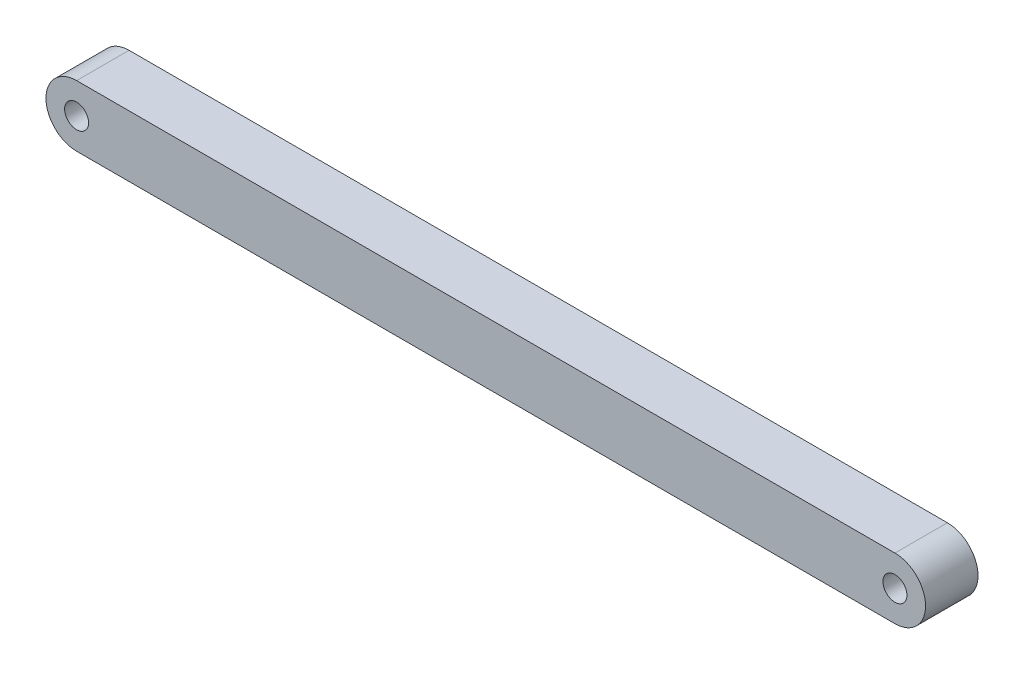
SolidWorks part; units mm, degrees
ref_plane "Front Plane" through (0, 0, 0) normal (0, 0, 1) x (1, 0, 0)
ref_plane "Top Plane" through (0, 0, 0) normal (0, 1, 0) x (1, 0, 0)
ref_plane "Right Plane" through (0, 0, 0) normal (1, 0, 0) x (0, 0, -1)
sketch "Sketch1" plane through (0, 0, 0) normal (0, 0, 1) x (1, 0, 0)
  line L0 (0, 0) -> (118.872, 0) construction
  line L1 (0, 4.445) -> (118.872, 4.445)
  line L2 (0, -4.445) -> (118.872, -4.445)
  arc A0 (0, 4.445) -> (0, -4.445) centre (0, 0) ccw
  arc A1 (118.872, -4.445) -> (118.872, 4.445) centre (118.872, 0) ccw
  point P3 (59.436, 0)
  dimension "D1" = 4.445
  dimension "D2" = 118.872
extrude "Boss-Extrude1" add sketch "Sketch1" along normal blind 7.62
sketch "Sketch2" plane through (0, 0, 7.62) normal (0, 0, 1) x (1, 0, 0)
  circle A0 centre (0, 0) radius 1.7399
  dimension "D1" = 3.4798
extrude "Cut-Extrude1" cut sketch "Sketch2" against normal through all both and the other way through all
ref_plane "Plane1" through (59.436, 0, 0) normal (1, 0, 0) x (0, 0, -1)
mirror "Mirror1" about plane through (59.436, 0, 0) normal (1, 0, 0) of "Cut-Extrude1"
